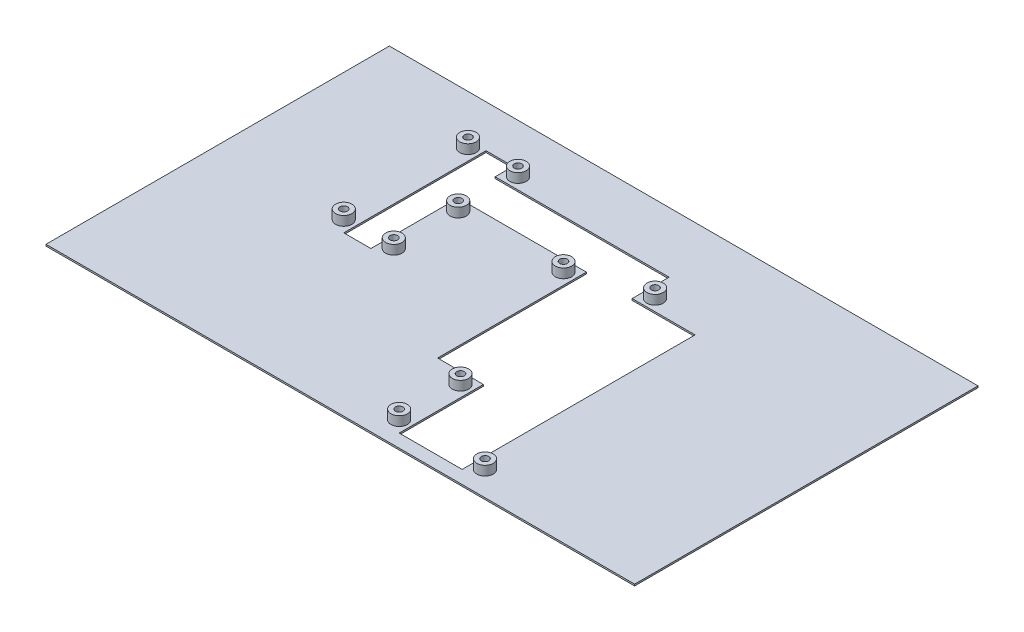
SolidWorks part; units mm, degrees
ref_plane "Front Plane" through (0, 0, 0) normal (0, 0, 1) x (1, 0, 0)
ref_plane "Top Plane" through (0, 0, 0) normal (0, 1, 0) x (1, 0, 0)
ref_plane "Right Plane" through (0, 0, 0) normal (1, 0, 0) x (0, 0, -1)
sketch "Sketch1" plane through (0, 0, 0) normal (0, 1, 0) x (1, 0, 0)
  line L4 (-201.4937, 0) -> (229.5472, 0) construction
  line L5 (0, -45.5) -> (28, -45.5)
  line L10 (0, 185.7213) -> (0, -147.4824) construction
  line L11 (180, 105) -> (-180, -105) construction
  line L16 (180, -105) -> (-180, 105) construction
  line L17 (28, -97) -> (28, -45.5)
  line L19 (66.5, -97) -> (66.5, -45.5)
  line L20 (66.5, -97) -> (28, -97)
  line L21 (-180, -105) -> (-180, 105)
  line L22 (180, 105) -> (-180, 105)
  line L23 (180, -105) -> (180, 105)
  line L24 (180, -105) -> (-180, -105)
  line L25 (0, -45.5) -> (0, 45.5)
  line L26 (28, 45.5) -> (66.5, 45.5)
  line L27 (66.5, -45.5) -> (66.5, 45.5)
  line L36 (-78.4, 68.1) -> (-78.4, 79.1)
  line L37 (-95, -7.9) -> (-78.4, -7.9)
  line L38 (-95, -7.9) -> (-95, 79.1)
  line L39 (-95, 79.1) -> (-78.4, 79.1)
  line L40 (-78.4, -7.9) -> (-78.4, 45.7333)
  line L41 (-78.4, 68.1) -> (28, 68.1)
  line L42 (-78.4, 45.7333) -> (-78.4, 45.5)
  line L43 (-78.4, 45.5) -> (0, 45.5)
  line L48 (28, 45.5) -> (28, 68.1)
  line L51 (-86.7824, 0) -> (-86.7, 79.1) construction
  point P0 (0, 0)
  point P3 (0, 0)
  point P5 (0, 0)
  point P22 (0, 0)
  dimension "D1" = 210
  dimension "D2" = 360
  dimension "D3" = 66.5
  dimension "D4" = 91
  dimension "D5" = 208
  dimension "D6" = 8
  dimension "D7" = 85
  dimension "D9" = 16.6
  dimension "D10" = 87
  dimension "D11" = 28
  dimension "D12" = 11
  dimension "D13" = 22.6
extrude "Boss-Extrude1" add sketch "Sketch1" along normal blind 1 contours L24 L23 L22 L21 L48 L26 L27 L19 L20 L17 L5 L25 L43 L40 L37 L38 L39 L36 L41
sketch "Sketch2" plane through (0, 1, 0) normal (0, 1, 0) x (1, 0, 0)
  line L0 (-106.8643, -7.9) -> (-39.2074, -7.9) construction
  line L1 (-78.4, 68.1) -> (28, 68.1) construction
  line L2 (-95, -7.9) -> (-95, 79.1) construction
  line L3 (-78.4, 68.1) -> (-78.4, 79.1) construction
  line L4 (-59.493, 75.1) -> (-110.149, 75.1) construction
  line L5 (-78.4, 45.5) -> (0, 45.5) construction
  line L6 (-78.4, -7.9) -> (-78.4, 45.5) construction
  line L7 (28, 45.5) -> (28, 68.1) construction
  line L8 (28, 45.5) -> (66.5, 45.5) construction
  line L9 (-95, -7.9) -> (-78.4, -7.9) construction
  line L10 (0, -45.5) -> (0, 45.5) construction
  line L11 (28, 45.5) -> (123.4571, 45.5) construction
  line L12 (66.5, -97) -> (66.5, 45.5) construction
  line L13 (28, -97) -> (28, -45.5) construction
  line L14 (0, -45.5) -> (28, -45.5) construction
  line L15 (0, -97) -> (93.983, -97) construction
  line L16 (66.5, -97) -> (28, -97) construction
  circle A1 centre (-71.4, 75.1) radius 7 construction
  circle A2 centre (-71.4, 75.1) radius 5
  circle A3 centre (-71.4, 75.1) radius 2.3
  circle A7 centre (-71.4, 38.5) radius 7 construction
  circle A8 centre (-71.4, 38.5) radius 5
  circle A9 centre (-71.4, 38.5) radius 2.3
  circle A10 centre (-102, 75.1) radius 7 construction
  circle A11 centre (-102, 75.1) radius 5
  circle A12 centre (-102, 75.1) radius 2.3
  circle A13 centre (-7, 38.5) radius 7 construction
  circle A14 centre (-7, 38.5) radius 5
  circle A15 centre (-7, 38.5) radius 2.3
  circle A16 centre (35, 52.5) radius 7 construction
  circle A17 centre (35, 52.5) radius 5
  circle A18 centre (35, 52.5) radius 2.3
  circle A19 centre (21, -52.5) radius 7 construction
  circle A20 centre (21, -52.5) radius 5
  circle A21 centre (21, -52.5) radius 2.3
  circle A22 centre (-71.4, -0.9) radius 7 construction
  circle A23 centre (-71.4, -0.9) radius 5
  circle A24 centre (-71.4, -0.9) radius 2.3
  circle A25 centre (-102, -0.9) radius 7 construction
  circle A26 centre (-102, -0.9) radius 5
  circle A27 centre (-102, -0.9) radius 2.3
  circle A31 centre (73.5, -90) radius 7 construction
  circle A32 centre (73.5, -90) radius 5
  circle A33 centre (73.5, -90) radius 2.3
  circle A34 centre (21, -90) radius 7 construction
  circle A35 centre (21, -90) radius 5
  circle A36 centre (21, -90) radius 2.3
  dimension "D1" = 14
  dimension "D2" = 10
  dimension "D3" = 4.6
  dimension "D4" = 14
  dimension "D5" = 10
  dimension "D6" = 4.6
  dimension "D7" = 14
  dimension "D8" = 10
  dimension "D9" = 4.6
  dimension "D10" = 14
  dimension "D11" = 10
  dimension "D12" = 4.6
  dimension "D13" = 14
  dimension "D14" = 10
  dimension "D15" = 4.6
  dimension "D16" = 14
  dimension "D17" = 10
  dimension "D18" = 4.6
  dimension "D19" = 14
  dimension "D20" = 10
  dimension "D21" = 4.6
  dimension "D22" = 14
  dimension "D23" = 10
  dimension "D24" = 4.6
  dimension "D28" = 14
  dimension "D29" = 10
  dimension "D30" = 4.6
  dimension "D31" = 14
  dimension "D32" = 10
  dimension "D33" = 4.6
extrude "Boss-Extrude2" add sketch "Sketch2" along normal blind 5.7 from surface at 0 starting at face at (-18.4714, 1, -12.5429)
